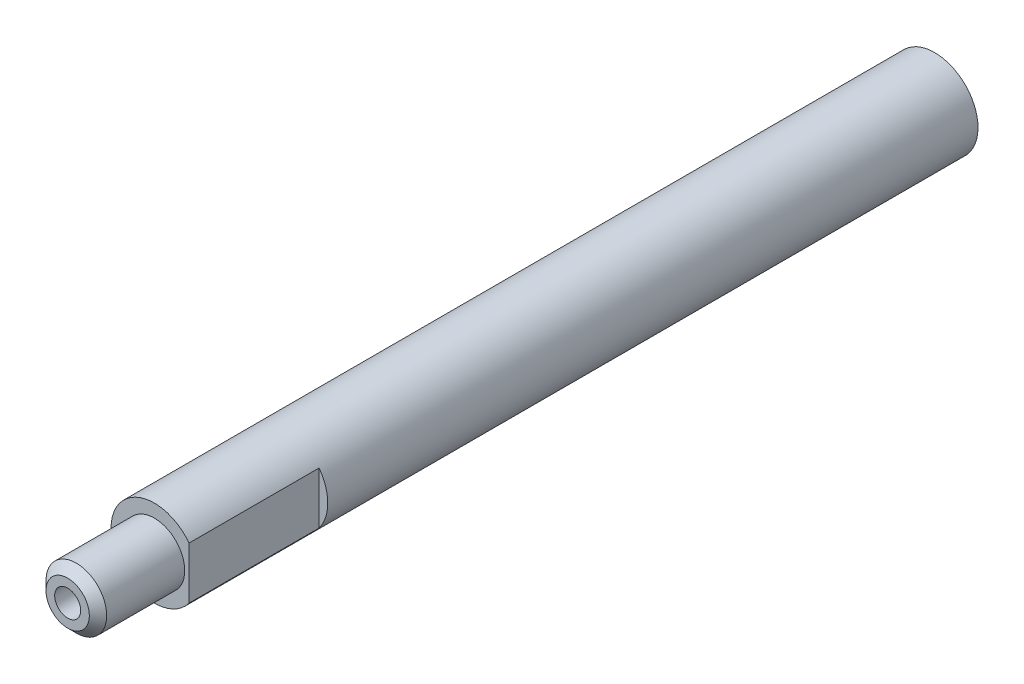
SolidWorks part; units mm, degrees
ref_plane "Front" through (0, 0, 0) normal (0, 0, 1) x (1, 0, 0)
ref_plane "Top" through (0, 0, 0) normal (0, 1, 0) x (1, 0, 0)
ref_plane "Right" through (0, 0, 0) normal (1, 0, 0) x (0, 0, -1)
sketch "Sketch1" plane through (0, 0, 0) normal (0, 0, 1) x (1, 0, 0)
  circle A0 centre (0, 0) radius 5
  dimension "D1" = 10
extrude "Base Extrude" add sketch "Sketch1" along normal blind 100
sketch "Sketch5" plane through (0, 0, 100) normal (0, 0, 1) x (1, 0, 0)
  circle A0 centre (0, 0) radius 3.5
  dimension "D1" = 7
extrude "Front Cut" cut sketch "Sketch5" against normal blind 10 flip side to cut
sketch "Sketch2" plane through (0, 0, 100) normal (0, 0, 1) x (1, 0, 0)
  circle A0 centre (0, 0) radius 1.5
  dimension "D1" = 3
extrude "Front Hole" cut sketch "Sketch2" against normal blind 10
chamfer "Chamfer1" distance 1 angle 45 1 edges at (3.5, 0, 100)
sketch "Sketch3" plane through (0, 0, 90) normal (0, 0, 1) x (1, 0, 0)
  line L0 (4, 3) -> (4, -3)
  arc A1 (4, -3) -> (4, 3) centre (0, 0) ccw
  circle A3 centre (0, 0) radius 5 construction
  dimension "D1" = 6
extrude "Keyway Cut" cut sketch "Sketch3" against normal blind 15
sketch "Sketch4" plane through (0, 0, 0) normal (0, 0, -1) x (-1, 0, 0)
  circle A0 centre (0, 0) radius 2
  dimension "D1" = 4
extrude "Back Hole" cut sketch "Sketch4" against normal blind 20
